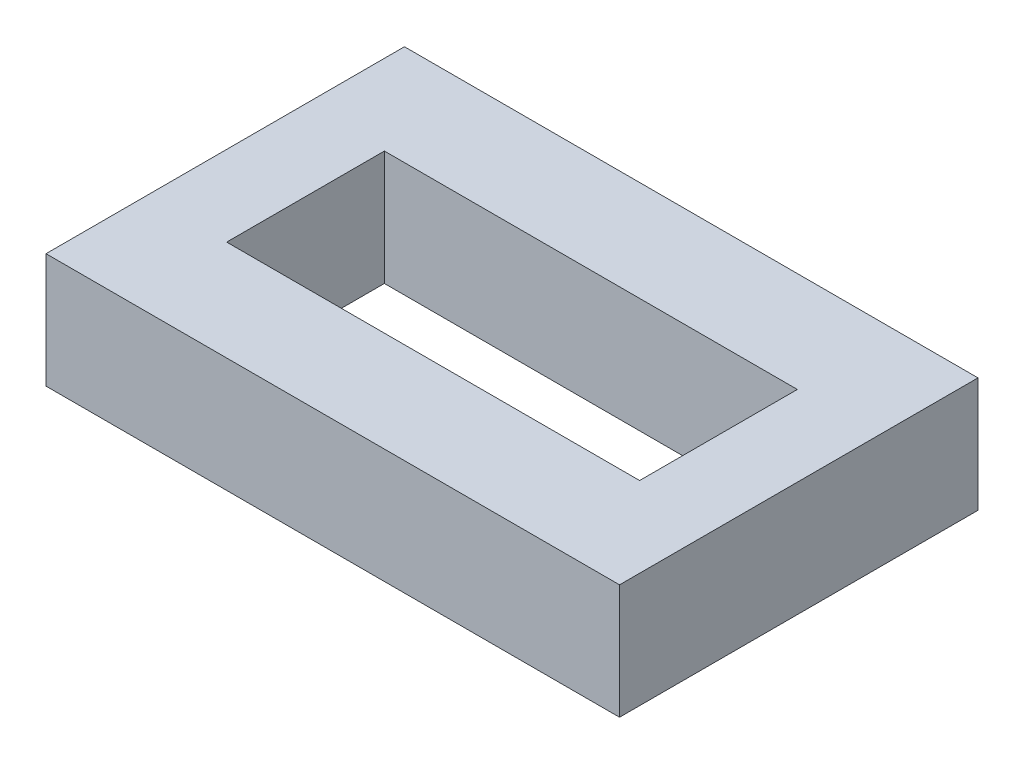
SolidWorks part; units mm, degrees
ref_plane "Front Plane" through (0, 0, 0) normal (0, 0, 1) x (1, 0, 0)
ref_plane "Top Plane" through (0, 0, 0) normal (0, 1, 0) x (1, 0, 0)
ref_plane "Right Plane" through (0, 0, 0) normal (1, 0, 0) x (0, 0, -1)
sketch "Sketch1" plane through (0, 0, 0) normal (0, 1, 0) x (1, 0, 0)
  line L1 (-25.4, -15.875) -> (25.4, -15.875)
  line L2 (-25.4, -15.875) -> (-25.4, 15.875)
  line L3 (-25.4, 15.875) -> (25.4, 15.875)
  line L4 (25.4, -15.875) -> (25.4, 15.875)
  line L5 (-25.4, -15.875) -> (25.4, 15.875) construction
  line L6 (-25.4, 15.875) -> (25.4, -15.875) construction
  line L7 (-18.288, -6.985) -> (18.288, -6.985)
  line L8 (-18.288, -6.985) -> (-18.288, 6.985)
  line L9 (-18.288, 6.985) -> (18.288, 6.985)
  line L10 (18.288, -6.985) -> (18.288, 6.985)
  line L11 (-18.288, -6.985) -> (18.288, 6.985) construction
  line L12 (-18.288, 6.985) -> (18.288, -6.985) construction
  point P0 (0, 0)
  point P6 (0, 0)
  dimension "D1" = 36.576
  dimension "D2" = 13.97
  dimension "D3" = 31.75
  dimension "D4" = 50.8
extrude "Boss-Extrude1" add sketch "Sketch1" along normal blind 10.16
